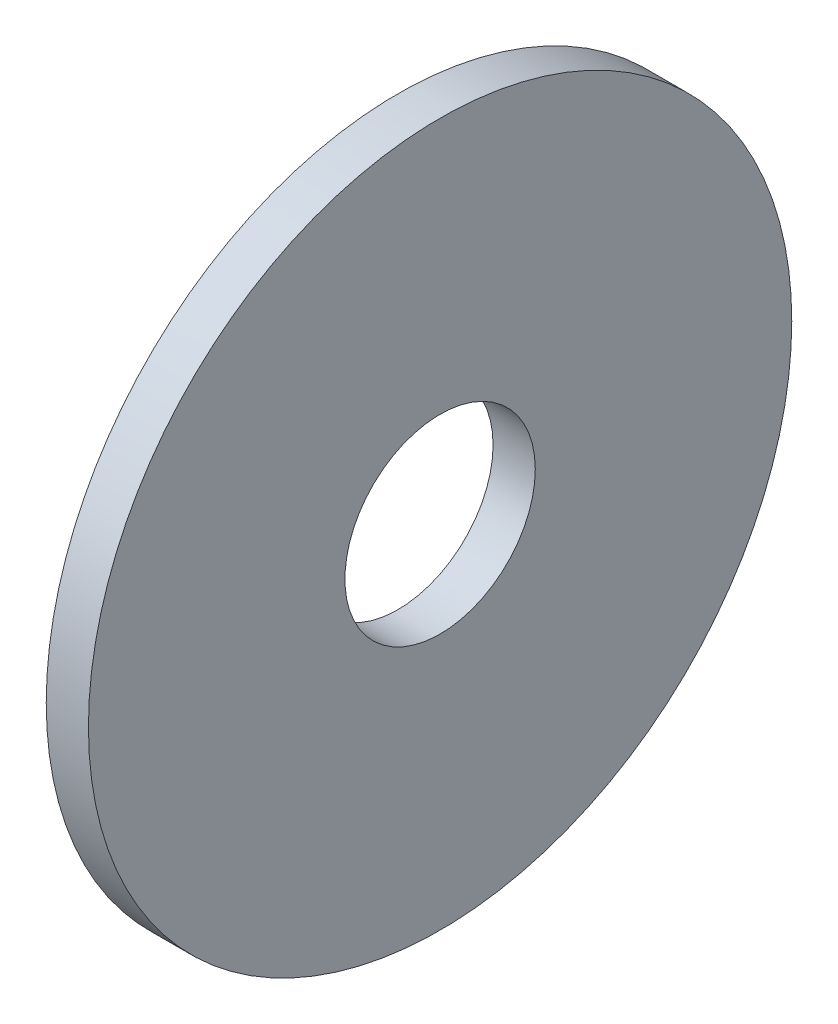
SolidWorks part; units mm, degrees
ref_plane "Front Plane" through (0, 0, 0) normal (0, 0, 1) x (1, 0, 0)
ref_plane "Top Plane" through (0, 0, 0) normal (0, 1, 0) x (1, 0, 0)
ref_plane "Right Plane" through (0, 0, 0) normal (1, 0, 0) x (0, 0, -1)
sketch "Sketch1" plane through (0, 0, 0) normal (1, 0, 0) x (0, 0, -1)
  circle A0 centre (0, 0) radius 9.525
  circle A1 centre (0, 0) radius 2.5781
  dimension "OD" = 19.05
  dimension "ID" = 5.1562
extrude "Boss-Extrude1" add sketch "Sketch1" along normal blind 1.143
